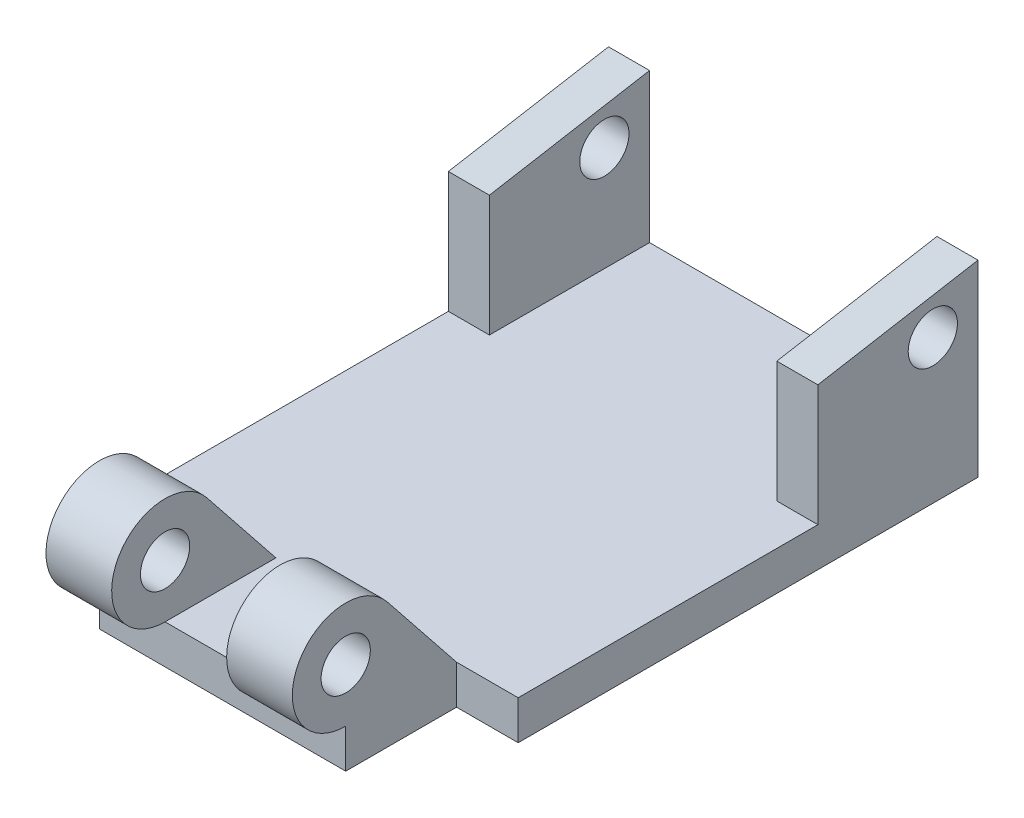
SolidWorks part; units mm, degrees
material "6061-T6 (SS)"
ref_plane "Front Plane" through (0, 0, 0) normal (0, 0, 1) x (1, 0, 0)
ref_plane "Top Plane" through (0, 0, 0) normal (0, 1, 0) x (1, 0, 0)
ref_plane "Right Plane" through (0, 0, 0) normal (1, 0, 0) x (0, 0, -1)
sketch "Sketch1" plane through (0, 0, 0) normal (0, 1, 0) x (1, 0, 0)
  line L1 (0, 0) -> (57.15, 0)
  line L2 (0, 0) -> (0, 71.12)
  line L3 (0, 71.12) -> (57.15, 71.12)
  line L4 (57.15, 0) -> (57.15, 71.12)
  line L5 (9.525, 0) -> (47.625, 0)
  line L6 (9.525, 0) -> (9.525, -17.145)
  line L7 (9.525, -17.145) -> (47.625, -17.145)
  line L8 (47.625, 0) -> (47.625, -17.145)
  dimension "D1" = 57.15
  dimension "D2" = 71.12
  dimension "D3" = 88.265
  dimension "D4" = 38.1
  dimension "D5" = 9.525
extrude "Boss-Extrude1" add sketch "Sketch1" along normal blind 6.0325 contours L1 L4 L3 L2 | L8 L1 L6 L7
sketch "Sketch2" plane through (9.525, 0, 0) normal (-1, 0, 0) x (0, 0, 1)
  line L0 (0, 6.0325) -> (10.6918, 19.4354)
  line L2 (0, 6.0325) -> (17.145, 6.0325) construction
  circle A1 centre (17.145, 14.2875) radius 8.255
  circle A2 centre (17.145, 14.2875) radius 3.81
  point P4 (11.4328, 20.247)
  point P9 (0, 0)
  point P10 (17.145, 13.1712)
  line M5 (17.145, 6.0325) -> (0, 6.0325)
  dimension "D1" = 4.445
  dimension "D2" = 7.62
extrude "Boss-Extrude2" add sketch "Sketch2" against normal up to surface (38.1 mm away) contours A1 L0 M5 | A1 A2 up to face at (47.625, 3.0162, 8.5725)
sketch "Sketch3" plane through (0, 6.0325, 0) normal (0, 1, 0) x (1, 0, 0)
  line L0 (47.625, 0) -> (9.525, 0) construction
  line L1 (9.525, 0) -> (19.685, 0)
  line L2 (9.525, 0) -> (9.525, -25.4)
  line L3 (9.525, -25.4) -> (19.685, -25.4)
  line L4 (19.685, 0) -> (19.685, -25.4)
  line L5 (9.525, -25.4) -> (47.625, -25.4) construction
  line L8 (47.625, 0) -> (37.465, 0)
  line L9 (47.625, 0) -> (47.625, -25.4)
  line L10 (47.625, -25.4) -> (37.465, -25.4)
  line L11 (37.465, 0) -> (37.465, -25.4)
  line L12 (19.685, 0) -> (37.465, 0)
  line L13 (19.685, 0) -> (19.685, -25.4)
  line L14 (19.685, -25.4) -> (37.465, -25.4)
  line L15 (37.465, 0) -> (37.465, -25.4)
  line M8 (9.525, 0) -> (47.625, 0)
  dimension "D1" = 10.16
  dimension "D2" = 10.16
extrude "Cut-Extrude1" cut sketch "Sketch3" along normal blind 35.7505 contours L4 L14 L11 M8
sketch "Sketch4" plane through (0, 0, 0) normal (-1, 0, 0) x (0, 0, 1)
  line L0 (-46.355, 6.0325) -> (-46.355, 24.765)
  line L1 (0, 6.0325) -> (-71.12, 6.0325) construction
  line L2 (-46.355, 24.765) -> (-71.12, 29.083)
  line L3 (-71.12, 29.083) -> (-71.12, 6.0325)
  line L4 (-71.12, 6.0325) -> (-46.355, 6.0325)
  line L5 (0, 0) -> (-71.12, 0) construction
  circle A0 centre (-64.135, 22.225) radius 3.81
  dimension "D6" = 7.62
  dimension "D1" = 24.765
  dimension "D2" = 29.083
  dimension "D3" = 24.765
  dimension "D4" = 22.225
  dimension "D5" = 6.985
extrude "Boss-Extrude3" add sketch "Sketch4" against normal up to surface (57.15 mm away) up to face at (57.15, 3.0162, -35.56)
sketch "Sketch5" plane through (0, 0, -71.12) normal (0, 0, -1) x (-1, 0, 0)
  line L0 (-57.15, 6.0325) -> (0, 6.0325) construction
  line L1 (-57.15, 6.0325) -> (0, 6.0325)
  line L2 (-57.15, 29.083) -> (0, 29.083) construction
  line L3 (-57.15, 6.0325) -> (-50.8, 6.0325)
  line L4 (-57.15, 6.0325) -> (-57.15, 29.083)
  line L5 (-57.15, 29.083) -> (-50.8, 29.083)
  line L6 (-50.8, 6.0325) -> (-50.8, 29.083)
  line L7 (-50.8, 29.083) -> (-6.35, 29.083)
  line L8 (0, 6.0325) -> (-6.35, 6.0325)
  line L9 (0, 6.0325) -> (0, 29.083)
  line L10 (0, 29.083) -> (-6.35, 29.083)
  line L11 (-6.35, 6.0325) -> (-6.35, 29.083)
  line M7 (0, 29.083) -> (-57.15, 29.083)
  dimension "D1" = 6.35
  dimension "D2" = 6.35
extrude "Cut-Extrude2" cut sketch "Sketch5" against normal blind 35.7505 contours L1 L11 L6 M7
